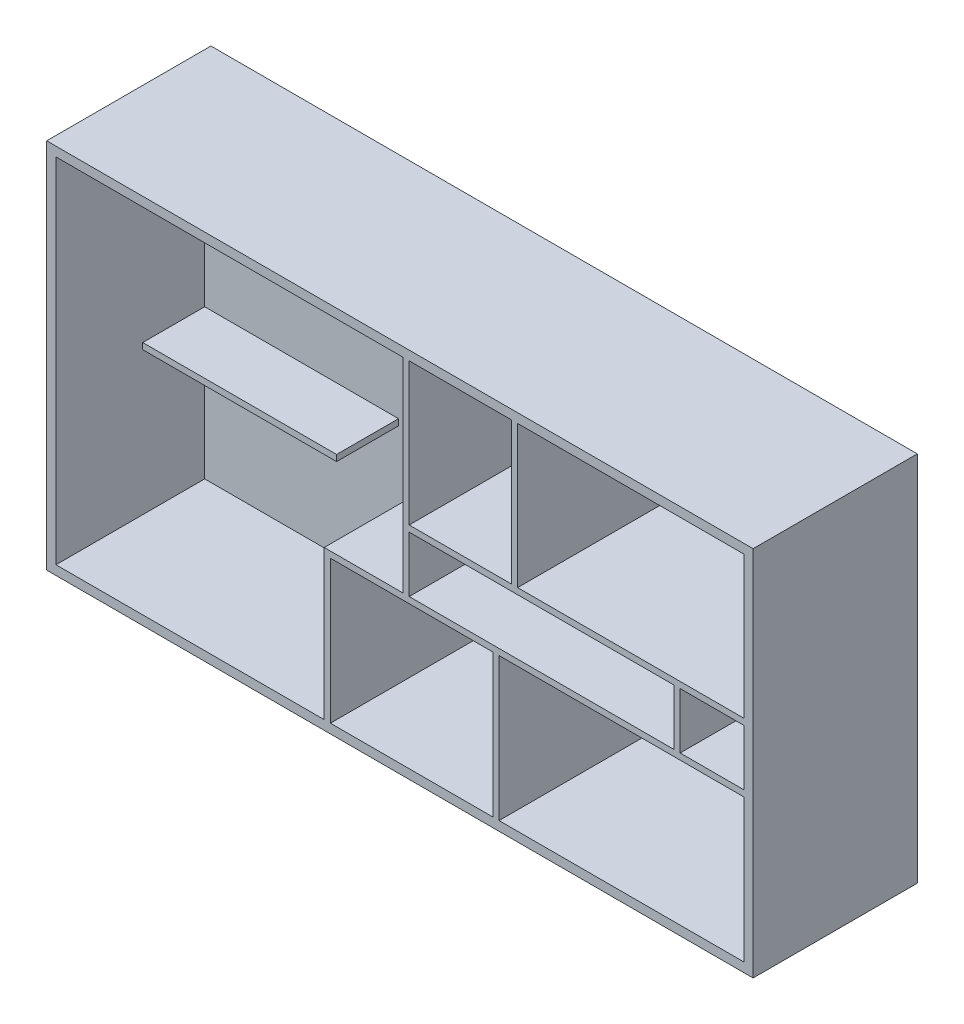
SolidWorks part; units mm, degrees
ref_plane "Front Plane" through (0, 0, 0) normal (0, 0, 1) x (1, 0, 0)
ref_plane "Top Plane" through (0, 0, 0) normal (0, 1, 0) x (1, 0, 0)
ref_plane "Right Plane" through (0, 0, 0) normal (1, 0, 0) x (0, 0, -1)
sketch "Sketch3" plane through (0, 0, 0) normal (0, 0, 1) x (1, 0, 0)
  line L0 (152.4, 152.4) -> (4550.005, 152.4)
  line L1 (0, 0) -> (11582.4, 0)
  line L2 (0, 0) -> (0, 6096)
  line L3 (0, 6096) -> (11582.4, 6096)
  line L4 (11582.4, 0) -> (11582.4, 6096)
  line L5 (4550.005, 152.4) -> (4550.005, 2596.7986)
  line L6 (4550.005, 2596.7986) -> (5842, 2596.7986)
  line L7 (11582.4, 6096) -> (7620, 6096) construction
  line L8 (7620, 6096) -> (5842, 6096) construction
  line L9 (5842, 5943.6) -> (5842, 3511.1986)
  line L10 (5943.6, 3511.1986) -> (10284.7543, 3511.1986)
  line L11 (7620, 5943.6) -> (7620, 3612.7986)
  line L12 (4550.005, 2596.7986) -> (5842, 2596.7986) construction
  line L13 (7315.2, 2495.1986) -> (7315.2, 152.4)
  line L14 (5842, 3511.1986) -> (5842, 2596.7986)
  line L15 (10386.3543, 3511.1986) -> (10386.3543, 2596.7986)
  line L16 (9786.5812, 3511.1986) -> (9786.5812, 2596.7986) construction
  line L17 (0, 6096) -> (0, 9448.8) construction
  line L18 (0, 9448.8) -> (6388.492, 9448.8) construction
  line L19 (6388.492, 9448.8) -> (6388.492, 6096) construction
  line L20 (11430, 152.4) -> (11430, 2495.1986)
  line L21 (3310.1163, 2590.8) -> (0, 2590.8) construction
  line L22 (152.4, 5943.6) -> (5842, 5943.6)
  line L23 (152.4, 152.4) -> (152.4, 5943.6)
  line L24 (4651.605, 152.4) -> (4651.605, 2495.1986)
  line L25 (4651.605, 2495.1986) -> (7315.2, 2495.1986)
  line L26 (7416.8, 2495.1986) -> (7416.8, 152.4)
  line L27 (10284.7543, 3511.1986) -> (10284.7543, 2596.7986)
  line L28 (5943.6, 3612.7986) -> (7620, 3612.7986)
  line L29 (5943.6, 5943.6) -> (5943.6, 3612.7986)
  line L30 (7721.6, 5943.6) -> (7721.6, 3612.7986)
  line L31 (7620, 6096) -> (7620, 3505.2) construction
  line L32 (7721.6, 6096) -> (7721.6, 3505.2) construction
  line L33 (5842, 6096) -> (5842, 3511.1986) construction
  line L34 (5943.6, 6096) -> (5943.6, 3511.1986) construction
  line L35 (5943.6, 5943.6) -> (7620, 5943.6)
  line L36 (152.4, 5943.6) -> (11430, 5943.6) construction
  line L37 (7721.6, 5943.6) -> (11430, 5943.6)
  line L38 (5842, 3612.7986) -> (11582.4, 3612.7986) construction
  line L39 (7721.6, 3612.7986) -> (11430, 3612.7986)
  line L40 (11430, 3612.7986) -> (11430, 5943.6)
  line L41 (11430, 152.4) -> (11430, 5943.6) construction
  line L42 (5842, 3511.1986) -> (11582.4, 3511.1986) construction
  line L43 (10386.3543, 3511.1986) -> (11430, 3511.1986)
  line L44 (10386.3543, 2596.7986) -> (11430, 2596.7986)
  line L45 (4550.005, 2596.7986) -> (11582.4, 2596.7986) construction
  line L46 (11430, 2596.7986) -> (11430, 3511.1986)
  line L47 (4651.605, 2495.1986) -> (11582.4, 2495.1986) construction
  line L48 (7315.2, 2596.7986) -> (7315.2, 0) construction
  line L49 (7416.8, 2596.7986) -> (7416.8, 0) construction
  line L50 (7416.8, 2495.1986) -> (11430, 2495.1986)
  line L51 (7416.8, 152.4) -> (11430, 152.4)
  line L52 (152.4, 152.4) -> (11430, 152.4) construction
  line L53 (4550.005, 0) -> (4550.005, 2596.7986) construction
  line L54 (4651.605, 0) -> (4651.605, 2495.1986) construction
  line L55 (4651.605, 152.4) -> (7315.2, 152.4)
  line L56 (5943.6, 3511.1986) -> (5943.6, 2596.7986)
  line L57 (5943.6, 2596.7986) -> (10284.7543, 2596.7986)
  line L58 (5943.6, 2596.7986) -> (7315.2, 2596.7986) construction
  dimension "D1" = 11582.4
  dimension "D2" = 6096
  dimension "D4" = 3962.4
  dimension "D5" = 1778
  dimension "D7" = 914.4
  dimension "D8" = 152.4
  dimension "D9" = 101.6
  dimension "D10" = 101.6
  dimension "D11" = 101.6
  dimension "D12" = 101.6
  dimension "D13" = 101.6
extrude "Boss-Extrude1" add sketch "Sketch3" along normal blind 2438.4 contours L1 L4 L3 L2 L55 L24 L25 L13 L51 L26 L50 L20 L46 L44 L15 L43 L40 L39 L30 L37 L10 L27 L6 L5 L0 L23 L22 L9 L29 L35 L11 L28
sketch "Sketch4" plane through (0, 0, 0) normal (0, 0, -1) x (-1, 0, 0)
  line L1 (-11582.4, 6096) -> (0, 6096)
  line L2 (-11582.4, 6096) -> (-11582.4, 0)
  line L3 (-11582.4, 0) -> (0, 0)
  line L4 (0, 6096) -> (0, 0)
extrude "Boss-Extrude2" add sketch "Sketch4" along normal blind 254
sketch "Sketch5" plane through (0, 0, 0) normal (0, 0, 1) x (1, 0, 0)
  line L1 (3330.805, 2596.7986) -> (152.4, 2596.7986)
  line L2 (152.4, 152.4) -> (152.4, 5943.6) construction
  line L3 (152.4, 2596.7986) -> (152.4, 2495.1986)
  line L4 (152.4, 152.4) -> (152.4, 5943.6) construction
  line L5 (152.4, 2495.1986) -> (3330.805, 2495.1986)
  line L6 (3330.805, 2495.1986) -> (3330.805, 2596.7986)
extrude "Boss-Extrude3" add sketch "Sketch5" along normal blind 1016
